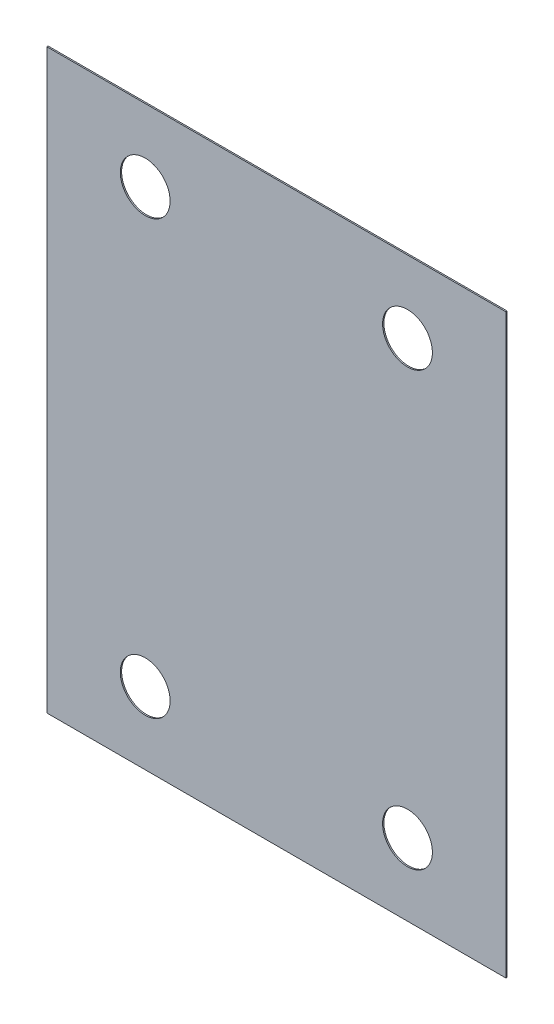
SolidWorks part; units mm, degrees
ref_plane "Спереди" through (0, 0, 0) normal (0, 0, 1) x (1, 0, 0)
ref_plane "Сверху" through (0, 0, 0) normal (0, 1, 0) x (1, 0, 0)
ref_plane "Справа" through (0, 0, 0) normal (1, 0, 0) x (0, 0, -1)
sketch "Эскиз1" plane through (0, 0, 0) normal (0, 0, 1) x (1, 0, 0)
  line L0 (175, -220) -> (175, 220)
  line L1 (175, 220) -> (-175, 220)
  line L2 (-175, 220) -> (-175, -220)
  line L3 (-175, -220) -> (175, -220)
  circle A4 centre (-100, 165) radius 19
  circle A5 centre (100, 165) radius 19
  circle A6 centre (100, -165) radius 19
  circle A7 centre (-100, -165) radius 19
extrude "Бобышка-Вытянуть1" add sketch "Эскиз1" along normal blind 1
